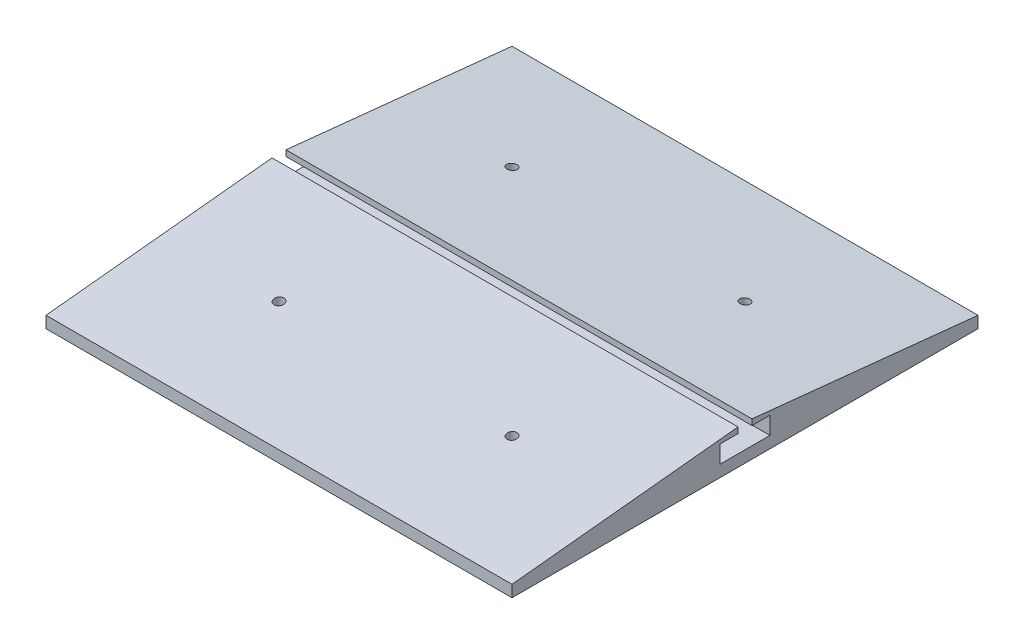
SolidWorks part; units mm, degrees
ref_plane "Front Plane" through (0, 0, 0) normal (0, 0, 1) x (1, 0, 0)
ref_plane "Top Plane" through (0, 0, 0) normal (0, 1, 0) x (1, 0, 0)
ref_plane "Right Plane" through (0, 0, 0) normal (1, 0, 0) x (0, 0, -1)
sketch "Sketch1" plane through (0, 0, 0) normal (0, 1, 0) x (1, 0, 0)
  line L1 (100, -100) -> (-100, -100)
  line L2 (100, -100) -> (100, 100)
  line L3 (100, 100) -> (-100, 100)
  line L4 (-100, -100) -> (-100, 100)
  line L5 (100, -100) -> (-100, 100) construction
  line L6 (100, 100) -> (-100, -100) construction
  point P0 (0, 0)
  dimension "D1" = 200
  dimension "D2" = 200
extrude "Boss-Extrude1" add sketch "Sketch1" along normal blind 5
sketch "Sketch9" plane through (100, 0, 0) normal (1, 0, 0) x (0, 0, -1)
  line L0 (-100, 5) -> (-3, 15)
  line L1 (-3, 15) -> (-3, 5)
  line L2 (-100, 5) -> (100, 5) construction
  line L3 (-3, 5) -> (-100, 5)
  line L4 (0, 0) -> (0, 15) construction
  line L5 (3, 5) -> (100, 5)
  line L6 (3, 15) -> (3, 5)
  line L7 (100, 5) -> (3, 15)
  dimension "D1" = 97
  dimension "D2" = 10
extrude "Boss-Extrude2" add sketch "Sketch9" against normal up to surface (200 mm away) up to face at (-100, 2.5, 0)
sketch "Sketch13" plane through (-100, 0, 0) normal (-1, 0, 0) x (0, 0, 1)
  line L0 (-3, 5) -> (3, 5) construction
  line L1 (-10.7, 12.5) -> (10.7, 12.5)
  line L2 (-10.7, 12.5) -> (-10.7, 5)
  line L3 (-10.7, 5) -> (10.7, 5)
  line L4 (10.7, 12.5) -> (10.7, 5)
  line L5 (0, 0) -> (0, 14.9801) construction
  dimension "D1" = 21.4
  dimension "D2" = 7.5
extrude "Cut-Extrude9" cut sketch "Sketch13" against normal up to next
sketch "Sketch17" plane through (0, 0, 0) normal (0, -1, 0) x (1, 0, 0)
  line L1 (50, -50) -> (-50, -50) construction
  line L2 (50, -50) -> (50, 50) construction
  line L3 (50, 50) -> (-50, 50) construction
  line L4 (-50, -50) -> (-50, 50) construction
  line L5 (50, -50) -> (-50, 50) construction
  line L6 (50, 50) -> (-50, -50) construction
  circle A0 centre (-50, 50) radius 2.1
  circle A1 centre (50, 50) radius 2.1
  circle A2 centre (50, -50) radius 2.1
  circle A3 centre (-50, -50) radius 2.1
  point P0 (0, 0)
  dimension "D2" = 4.2
  dimension "D1" = 100
  dimension "D3" = 2
  dimension "D4" = 2
sketch "Sketch18" plane through (0, 0, 0) normal (0, -1, 0) x (1, 0, 0)
  line L1 (50, -50) -> (-50, -50) construction
  line L2 (50, -50) -> (50, 50) construction
  line L3 (50, 50) -> (-50, 50) construction
  line L4 (-50, -50) -> (-50, 50) construction
  line L5 (50, -50) -> (-50, 50) construction
  line L6 (50, 50) -> (-50, -50) construction
  line L9 (-52.1362, 46.3) -> (-47.8638, 46.3)
  line L10 (-47.8638, 46.3) -> (-45.7276, 50)
  line L11 (-45.7276, 50) -> (-47.8638, 53.7)
  line L12 (-47.8638, 53.7) -> (-52.1362, 53.7)
  line L14 (47.8638, 46.3) -> (52.1362, 46.3)
  line L15 (52.1362, 46.3) -> (54.2724, 50)
  line L16 (54.2724, 50) -> (52.1362, 53.7)
  line L17 (52.1362, 53.7) -> (47.8638, 53.7)
  line L20 (47.8638, -53.7) -> (52.1362, -53.7)
  line L21 (52.1362, -53.7) -> (54.2724, -50)
  line L22 (54.2724, -50) -> (52.1362, -46.3)
  line L23 (52.1362, -46.3) -> (47.8638, -46.3)
  line L26 (-52.1362, -53.7) -> (-47.8638, -53.7)
  line L27 (-47.8638, -53.7) -> (-45.7276, -50)
  line L28 (-45.7276, -50) -> (-47.8638, -46.3)
  line L29 (-47.8638, -46.3) -> (-52.1362, -46.3)
  line L30 (-52.1362, 46.3) -> (-54.2724, 46.3)
  line L31 (-54.2724, 46.3) -> (-54.2724, 53.7)
  line L32 (-54.2724, 53.7) -> (-52.1362, 53.7)
  line L33 (-52.1362, -53.7) -> (-54.2724, -53.7)
  line L34 (-54.2724, -53.7) -> (-54.2724, -46.3)
  line L35 (-54.2724, -46.3) -> (-52.1362, -46.3)
  line L36 (47.8638, -53.7) -> (45.7276, -53.7)
  line L37 (45.7276, -53.7) -> (45.7276, -46.3)
  line L38 (45.7276, -46.3) -> (47.8638, -46.3)
  line L39 (47.8638, 46.3) -> (45.7276, 46.3)
  line L40 (45.7276, 46.3) -> (45.7276, 53.7)
  line L41 (45.7276, 53.7) -> (47.8638, 53.7)
  line L49 (-54.2724, 50) -> (-53.2043, 48.15) [skipped]
  line L50 (-52.1362, 53.7) -> (-53.2043, 51.85) [skipped]
  circle A0 centre (-50, 50) radius 3.7 construction
  circle A1 centre (50, 50) radius 3.7 construction
  circle A2 centre (50, -50) radius 3.7 construction
  circle A3 centre (-50, -50) radius 3.7 construction
  point P0 (0, 0)
  dimension "D1" = 100
  dimension "D2" = 7.4
  dimension "D3" = 2
  dimension "D4" = 2
extrude "Cut-Extrude14" cut sketch "Sketch18" against normal blind 3.6 from offset 2 offset against normal yes
extrude "Cut-Extrude15" cut sketch "Sketch17" against normal through all
move or copy body "Body-Move/Copy1" bodies to move or copy 110 parameters "D1"=0, "D2"=0, "D3"=0
